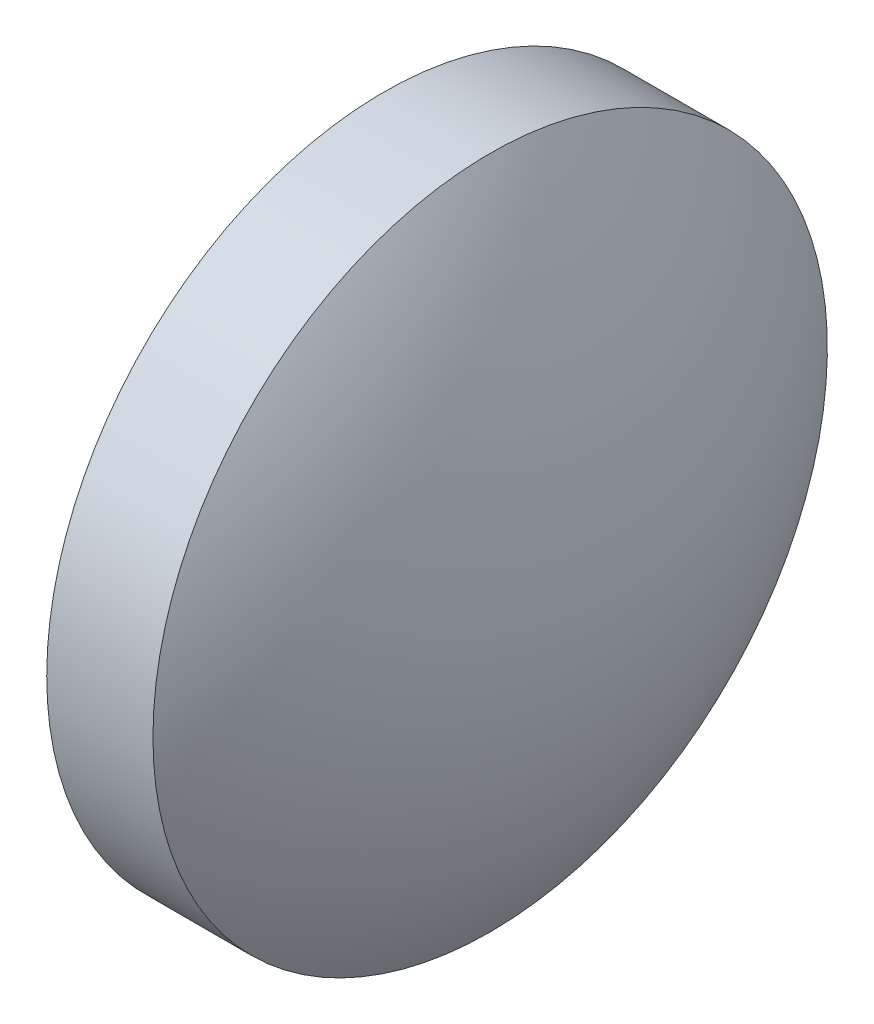
SolidWorks part; units mm, degrees
ref_plane "前视基准面" through (0, 0, 0) normal (0, 0, 1) x (1, 0, 0)
ref_plane "上视基准面" through (0, 0, 0) normal (0, 1, 0) x (1, 0, 0)
ref_plane "右视基准面" through (0, 0, 0) normal (1, 0, 0) x (0, 0, -1)
sketch "草图1" plane through (0, 0, 0) normal (0, 0, 1) x (1, 0, 0)
  line L0 (350.1418, -36.8605) -> (361.4451, -36.8605) construction
  line L1 (352.4698, -36.8605) -> (352.4698, -30.5105)
  line L2 (352.4698, -30.5105) -> (354.4698, -30.5105)
  line L3 (356.3898, -36.8605) -> (352.4698, -36.8605)
  arc A0 (356.3898, -36.8605) -> (354.4698, -30.5105) centre (344.9292, -36.8605) ccw
revolve "旋转1" add sketch "草图1" angle 360 about L0
